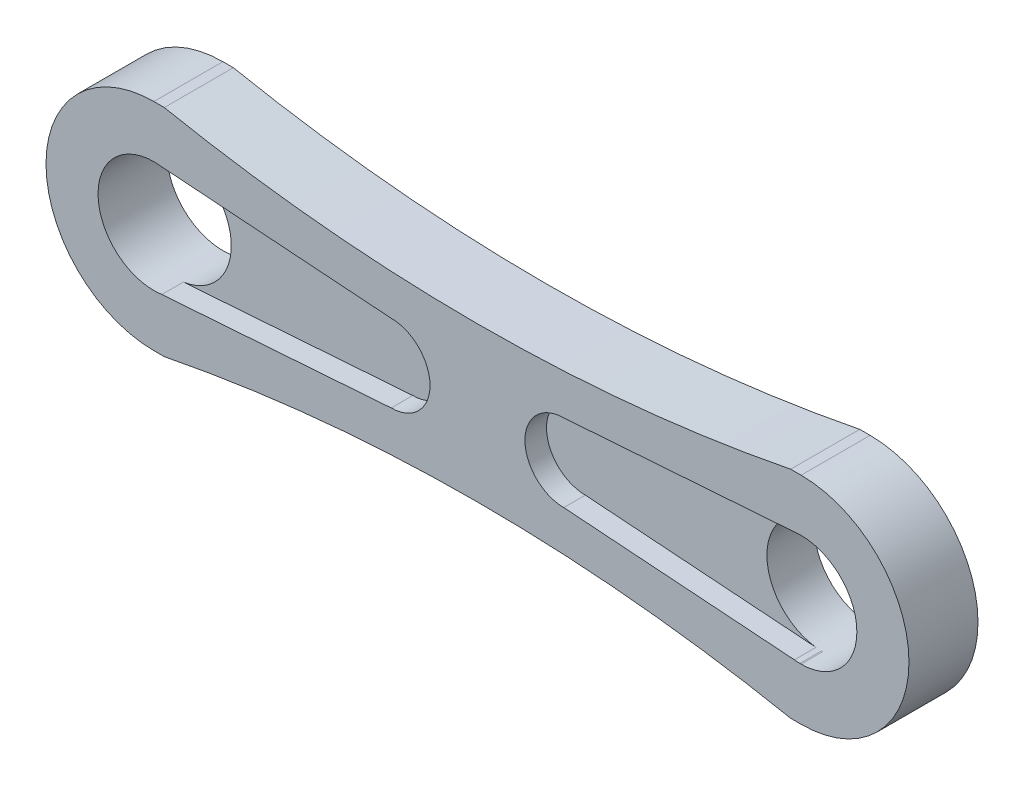
SolidWorks part; units mm, degrees
ref_plane "Front Plane" through (0, 0, 0) normal (0, 0, 1) x (1, 0, 0)
ref_plane "Top Plane" through (0, 0, 0) normal (0, 1, 0) x (1, 0, 0)
ref_plane "Right Plane" through (0, 0, 0) normal (1, 0, 0) x (0, 0, -1)
sketch "Sketch1" plane through (0, 0, 0) normal (0, 0, 1) x (1, 0, 0)
  line L1 (-19.05, 6.35) -> (19.05, 6.35)
  line L2 (-19.05, 6.35) -> (-19.05, -6.35)
  line L3 (-19.05, -6.35) -> (19.05, -6.35)
  line L4 (19.05, 6.35) -> (19.05, -6.35)
  arc A0 (-19.05, 6.35) -> (-19.05, -6.35) centre (-19.05, 0) ccw
  arc A1 (19.05, -6.35) -> (19.05, 6.35) centre (19.05, 0) ccw
  circle A2 centre (-19.05, 0) radius 3.2869
  circle A3 centre (19.05, 0) radius 3.2823
  point P0 (0, 0)
  dimension "D1" = 38.1
  dimension "D2" = 12.7
extrude "Boss-Extrude2" add sketch "Sketch1" along normal blind 4.064 contours A2 L2 A0 | A3 L4 L1 L2 A2 L3 | A3 L4 A1
sketch "Sketch2" plane through (0, 0, 4.064) normal (0, 0, 1) x (1, 0, 0)
  line L0 (0, -6.35) -> (0, 12.1666) construction
  line L1 (-19.05, 3.2869) -> (-5.08, 2.286)
  line L2 (-19.05, -3.2869) -> (-5.08, -2.286)
  line L3 (-19.05, 3.2869) -> (-19.05, -3.2869)
  line L5 (-19.05, -6.35) -> (19.05, -6.35) construction
  line L6 (19.05, -3.2869) -> (5.08, -2.286)
  line L7 (19.05, 3.2869) -> (19.05, -3.2869)
  line L8 (19.05, 3.2869) -> (5.08, 2.286)
  arc A0 (-5.08, -2.286) -> (-5.08, 2.286) centre (-5.08, 0) ccw
  circle A1 centre (-19.05, 0) radius 3.2869 construction
  arc A2 (5.08, -2.286) -> (5.08, 2.286) centre (5.08, 0) cw
  circle A3 centre (19.05, 0) radius 3.2823 construction
  point P4 (-5.08, 0)
  point P22 (-19.05, 0)
  dimension "D2" = 4.572
  dimension "D3" = 13.97
  dimension "D1" = 13.97
extrude "Cut-Extrude1" cut sketch "Sketch2" against normal blind 1.27
sketch "Sketch4" plane through (0, 0, 4.064) normal (0, 0, 1) x (1, 0, 0)
  line L0 (-5.08, 2.286) -> (-18.5814, 3.2533) construction
  line L2 (-19.05, 0) -> (19.05, 0) construction
  circle A0 centre (0, 99.4309) radius 94.8894
  circle A1 centre (-19.05, 0) radius 6.35
  circle A2 centre (19.05, 0) radius 6.35
  arc A3 (19.05, -6.35) -> (19.05, 6.35) centre (19.05, 0) ccw construction
  arc A6 (-19.05, 6.35) -> (-19.05, -6.35) centre (-19.05, 0) ccw construction
  circle A8 centre (0, -99.4309) radius 94.8894
  point P13 (-11.8307, 2.7697)
  line M17 (19.05, 6.35) -> (-19.05, 6.35)
  line M19 (-19.05, -6.35) -> (19.05, -6.35)
extrude "Cut-Extrude2" cut sketch "Sketch4" against normal through all contours A0 M17 | A8 M19
